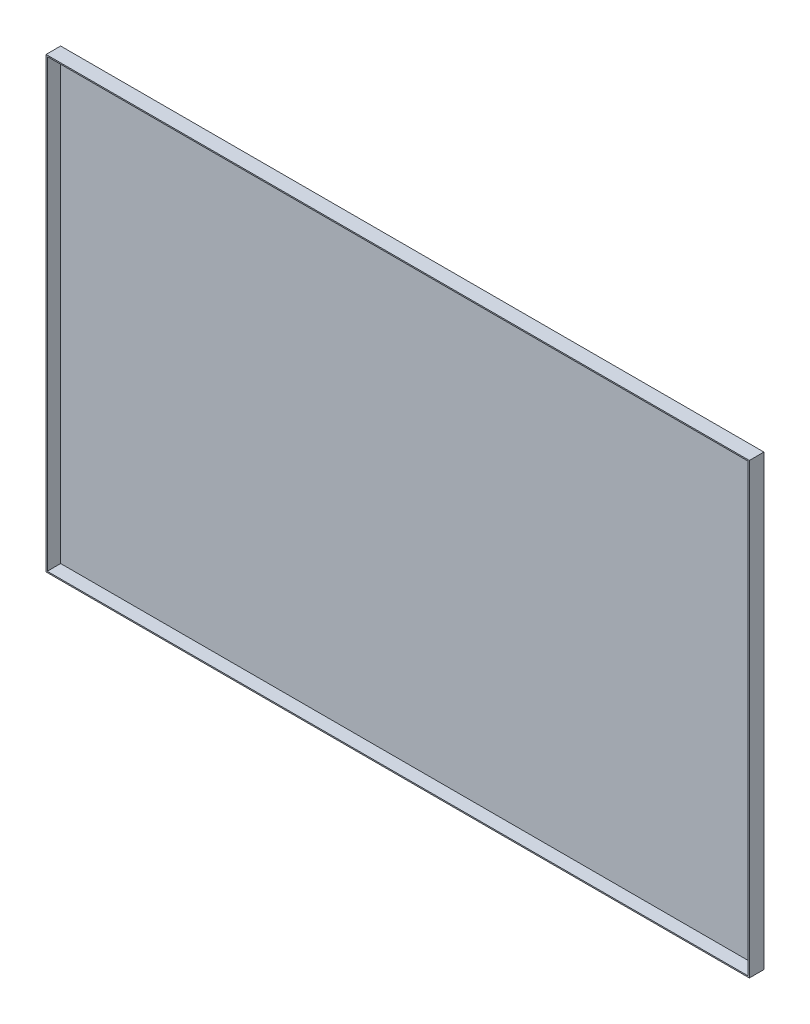
SolidWorks part; units mm, degrees
ref_plane "前视基准面" through (0, 0, 0) normal (0, 0, 1) x (1, 0, 0)
ref_plane "上视基准面" through (0, 0, 0) normal (0, 1, 0) x (1, 0, 0)
ref_plane "右视基准面" through (0, 0, 0) normal (1, 0, 0) x (0, 0, -1)
sketch "草图1" plane through (0, 0, 0) normal (0, 0, 1) x (1, 0, 0)
  line L1 (-289.5, 184.5) -> (289.5, 184.5)
  line L2 (-289.5, 184.5) -> (-289.5, -184.5)
  line L3 (-289.5, -184.5) -> (289.5, -184.5)
  line L4 (289.5, 184.5) -> (289.5, -184.5)
  line L5 (-289.5, 184.5) -> (289.5, -184.5) construction
  line L6 (-289.5, -184.5) -> (289.5, 184.5) construction
  point P0 (0, 0)
  dimension "D1" = 579
  dimension "D2" = 369
extrude "凸台-拉伸1" add sketch "草图1" along normal blind 12
shell "抽壳1" thickness 1
